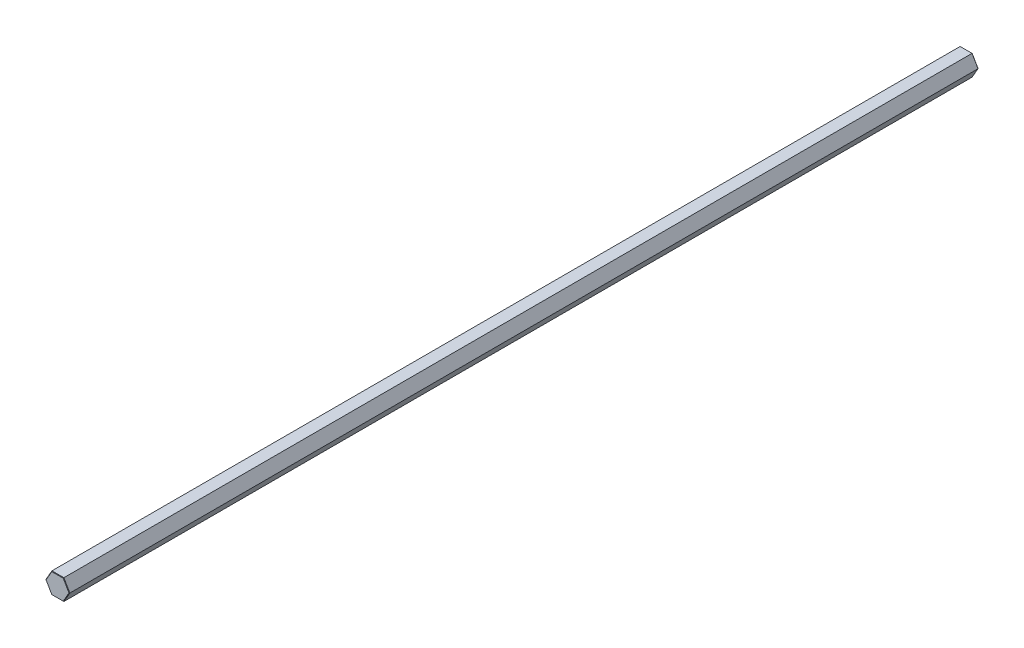
SolidWorks part; units mm, degrees
material "6061 Alloy"
ref_plane "Front Plane" through (0, 0, 0) normal (0, 0, 1) x (1, 0, 0)
ref_plane "Top Plane" through (0, 0, 0) normal (0, 1, 0) x (1, 0, 0)
ref_plane "Right Plane" through (0, 0, 0) normal (1, 0, 0) x (0, 0, -1)
ref_plane "Plane1" through (0, 0, 0) normal (0, 0, -1) x (-1, 0, 0)
sketch "Sketch1" plane through (0, 0, 0) normal (0, 0, -1) x (-1, 0, 0)
  line L0 (3.6662, 6.35) -> (-3.6662, 6.35)
  line L1 (-3.6662, 6.35) -> (-7.3323, 0)
  line L2 (-7.3323, 0) -> (-3.6662, -6.35)
  line L3 (-3.6662, -6.35) -> (3.6662, -6.35)
  line L4 (3.6662, -6.35) -> (7.3323, 0)
  line L5 (7.3323, 0) -> (3.6662, 6.35)
extrude "Boss-Extrude1" add sketch "Sketch1" against normal blind 558.8
chamfer "Chamfer1" distance 0.254 angle 45 12 edges at (0, -6.35, 0) (5.4993, -3.175, 0) (-5.4993, -3.175, 0) (5.4993, 3.175, 0) (-5.4993, 3.175, 0) (0, 6.35, 0) (-5.4993, -3.175, 558.8) (0, -6.35, 558.8) (-5.4993, 3.175, 558.8) (5.4993, -3.175, 558.8) (0, 6.35, 558.8) (5.4993, 3.175, 558.8)
